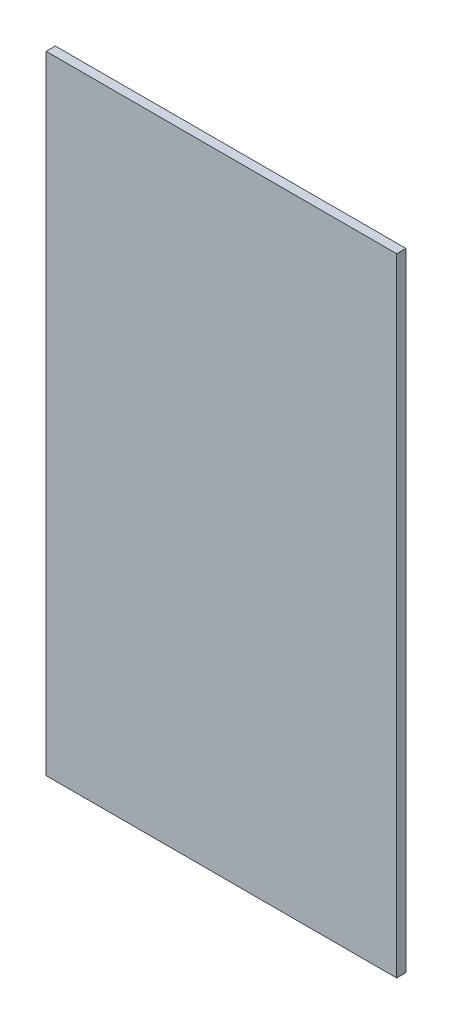
SolidWorks part; units mm, degrees
ref_plane "Plan de face" through (0, 0, 0) normal (0, 0, 1) x (1, 0, 0)
ref_plane "Plan de dessus" through (0, 0, 0) normal (0, 1, 0) x (1, 0, 0)
ref_plane "Plan de droite" through (0, 0, 0) normal (1, 0, 0) x (0, 0, -1)
sketch "Esquisse1" plane through (0, 0, 0) normal (0, 0, 1) x (1, 0, 0)
  line L1 (-190, 340) -> (190, 340)
  line L2 (-190, 340) -> (-190, -340)
  line L3 (-190, -340) -> (190, -340)
  line L4 (190, 340) -> (190, -340)
  dimension "D1" = 380
  dimension "D2" = 680
  dimension "D3" = 340
  dimension "D4" = 190
extrude "Boss.-Extru.1" add sketch "Esquisse1" along normal blind 10
